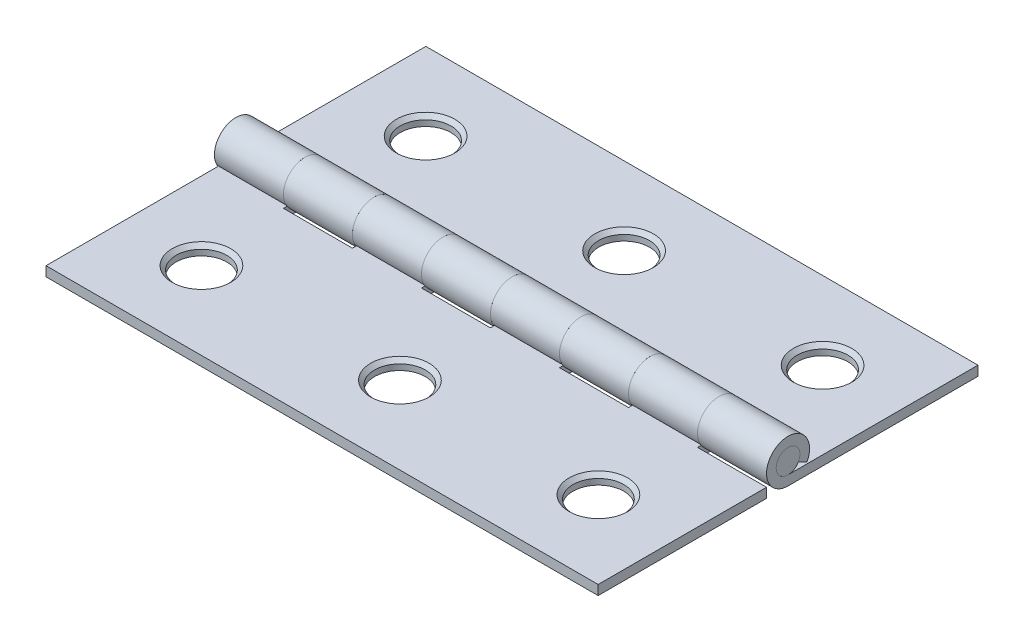
SolidWorks part; units mm, degrees
ref_plane "Front Plane" through (0, 0, 0) normal (0, 0, 1) x (1, 0, 0)
ref_plane "Top Plane" through (0, 0, 0) normal (0, 1, 0) x (1, 0, 0)
ref_plane "Right Plane" through (0, 0, 0) normal (1, 0, 0) x (0, 0, -1)
sketch "Sketch1" plane through (0, 0, 0) normal (0, 1, 0) x (1, 0, 0)
  line L0 (-25.4, 0) -> (25.4, 0) construction
  line L1 (-25.4, -17.4752) -> (-25.4, 17.4752) construction
  line L2 (-25.4, -17.4752) -> (-18.2626, -17.4752) construction
  line L3 (-18.2626, -17.4752) -> (0, -17.4752) construction
  line L4 (0, -17.4752) -> (18.2626, -17.4752) construction
  line L5 (25.4, -17.4752) -> (25.4, -10.3124) construction
  line L6 (18.2626, -17.4752) -> (25.4, -17.4752) construction
  line L7 (-25.4, 17.4752) -> (-18.2626, 17.4752) construction
  line L8 (-18.2626, 17.4752) -> (0, 17.4752) construction
  line L9 (0, 17.4752) -> (18.2626, 17.4752) construction
  line L10 (18.2626, 17.4752) -> (25.4, 17.4752) construction
  line L11 (18.2626, -13.0048) -> (18.2626, -7.62) construction
  line L12 (18.2626, -10.3124) -> (25.4, -10.3124) construction
  point P3 (18.2626, -12.6492)
  point P4 (0, 0)
  point P8 (-25.4, 0)
  point P17 (-19.05, 0)
  point P21 (18.2626, -10.3124)
  dimension "Frame Leaf Height" = 50.8
  dimension "Overall Width" = 34.9504
  dimension "Hole to End 1" = 7.1374
  dimension "Hole Spacing" = 18.2626
  dimension "D3" = 18.2626
  dimension "Hole to End 2" = 7.1374
  dimension "D1" = 7.1374
  dimension "D2" = 7.1374
  dimension "D4" = 18.2626
  dimension "D6" = 18.2626
  dimension "Knuckle Length" = 6.35
  dimension "Hole Chamfer Dia" = 5.3848
  dimension "Hole Center to Pin" = 10.3124
  dimension "Door Leaf Height" = 50.8
  dimension "Frame Leaf Width" = 17.4752
  dimension "Door Leaf Width" = 17.4752
  dimension "Mounting Hole Diameter" = 4.6736
sketch "Sketch2" plane through (0, 0, 0) normal (1, 0, 0) x (0, 0, -1)
  line L2 (0, -1.9812) -> (0, -1.0922) construction
  line L4 (0, 1.0922) -> (0, -1.0922) construction
  point P8 (0, 0)
  dimension "Leaf Thickness" = 0.889
  dimension "Pin Diameter" = 2.1844
sketch "Sketch3" plane through (0, 0, 0) normal (1, 0, 0) x (0, 0, -1)
  line L3 (0, 0) -> (-1.9812, -1.0922) construction
  line L4 (0, -1.9812) -> (-17.4752, -1.9812)
  line L5 (-17.4752, -1.9812) -> (-17.4752, -1.0922)
  line L7 (-17.4752, -1.0922) -> (0, -1.0922)
  line L8 (-17.4752, 0) -> (17.4752, 0) construction
  line L9 (-0.9565, -0.5273) -> (-1.735, -0.9565)
  line L11 (-1.9812, 0) -> (-1.9812, -1.0922) construction
  circle A4 centre (0, 0) radius 1.0922 construction
  circle A5 centre (0, 0) radius 1.9812 construction
  arc A8 (-0.9565, -0.5273) -> (0, -1.0922) centre (0, 0) cw
  arc A9 (-1.735, -0.9565) -> (0, -1.9812) centre (0, 0) cw
  point P0 (-1.735, -0.9565)
  point P13 (-0.9565, -0.5273)
extrude "Boss-Extrude1" add sketch "Sketch3" along normal mid plane 50.8
sketch "Sketch4" plane through (0, 0, 0) normal (0, 1, 0) x (1, 0, 0)
  line L0 (-25.4, -1.9812) -> (25.4, -1.9812) construction
  line L1 (-25.4, -1.9812) -> (25.4, -1.9812) construction
  line L2 (25.4, 1.9812) -> (-25.4, 1.9812) construction
  line L3 (25.4, 1.9812) -> (-25.4, 1.9812) construction
  line L4 (-19.05, -1.9812) -> (-19.05, 1.9812)
  line L6 (-19.05, 1.9812) -> (-12.7, 1.9812)
  line L7 (-12.7, -1.9812) -> (-19.05, -1.9812)
  line L8 (-12.7, 1.9812) -> (-12.7, -1.9812)
  point P8 (-19.05, 0)
  dimension "D1" = 6.35
extrude "Cut-Extrude1" cut sketch "Sketch4" against normal through all both and the other way through all
pattern_linear "LPattern1" count 6 spacing 12.7 along (1, 0, 0) of "Cut-Extrude1"
sketch "Sketch5" plane through (0, -1.0922, 0) normal (0, 1, 0) x (1, 0, 0)
  line L0 (18.2626, -10.3124) -> (-18.2626, -10.3124) construction
  line L1 (0, -10.3124) -> (0, -17.4752) construction
  line L2 (-18.2626, -10.3124) -> (-18.2626, -17.4752) construction
  circle A0 centre (18.2626, -10.3124) radius 2.6924
  circle A1 centre (0, -10.3124) radius 2.6924
  circle A2 centre (-18.2626, -10.3124) radius 2.6924
extrude "Cut-Extrude2" cut sketch "Sketch5" against normal through all draft 45
sketch "Sketch9" plane through (0, 0, 0) normal (0, 1, 0) x (1, 0, 0)
  circle A0 centre (18.2626, -10.3124) radius 2.3368
  circle A1 centre (0, -10.3124) radius 2.3368
  circle A2 centre (-18.2626, -10.3124) radius 2.3368
  dimension "D1" = 4.6736
extrude "Cut-Extrude3" cut sketch "Sketch9" against normal through all both and the other way through all
pattern_circular "CirPattern1" count 2 over 360 about axis through (0, 0, 0) along (0, 1, 0) of bodies 110 107
sketch "Sketch6" plane through (0, 0, 0) normal (1, 0, 0) x (0, 0, -1)
  circle A0 centre (0, 0) radius 1.0922
  dimension "D1" = 2.1844
extrude "Boss-Extrude2" add sketch "Sketch6" along normal mid plane 50.8 separate body
sketch "Sketch7" plane through (0, 0, 0) normal (1, 0, 0) x (0, 0, -1)
  line L0 (-1.0922, 0) -> (1.0922, 0) construction
  line L1 (-17.4752, 0) -> (17.4752, 0) construction
  line L2 (17.4752, -1.0922) -> (17.4752, -1.9812) construction
  line L3 (17.4752, -1.0922) -> (17.4752, -1.9812) construction
  line L4 (17.4752, -1.9812) -> (-17.4752, -1.9812) construction
  line L5 (-17.4752, -1.9812) -> (-17.4752, -1.0922)
  point P6 (0, 0)
  point P8 (1.0922, 0)
  point P9 (-1.0922, 0)
  point P12 (17.4752, -1.0922)
  point P13 (17.4752, -1.9812)
  point P14 (-17.4752, -1.9812)
  dimension "D1" = 2.1844
  dimension "D2" = 34.9504
  dimension "D3" = 0.889
sketch "Sketch8" plane through (0, 0, 0) normal (0, 1, 0) x (1, 0, 0)
  line L0 (-20.955, -10.3124) -> (-15.5702, -10.3124) construction
  line L1 (-2.6924, -10.3124) -> (2.6924, -10.3124) construction
  line L2 (15.5702, -10.3124) -> (20.955, -10.3124) construction
  line L3 (-18.2626, -7.62) -> (-18.2626, -13.0048) construction
  line L4 (0, -7.62) -> (0, -13.0048) construction
  line L5 (18.2626, -7.62) -> (18.2626, -13.0048) construction
  line L6 (-18.2626, 13.0048) -> (-18.2626, 7.62) construction
  line L7 (-20.955, 10.3124) -> (-15.5702, 10.3124) construction
  line L8 (0, 13.0048) -> (0, 7.62) construction
  line L9 (-2.6924, 10.3124) -> (2.6924, 10.3124) construction
  line L10 (18.2626, 13.0048) -> (18.2626, 7.62) construction
  line L11 (15.5702, 10.3124) -> (20.955, 10.3124) construction
  line L12 (18.2626, 10.3124) -> (20.1664, 12.2162) construction
  circle A1 centre (-18.2626, -10.3124) radius 2.6924 construction
  circle A2 centre (0, -10.3124) radius 2.6924 construction
  circle A3 centre (18.2626, -10.3124) radius 2.6924 construction
  circle A4 centre (-18.2626, 10.3124) radius 2.6924 construction
  circle A5 centre (0, 10.3124) radius 2.6924 construction
  circle A6 centre (18.2626, 10.3124) radius 2.6924 construction
  circle A7 centre (18.2626, 10.3124) radius 2.6924 construction
  point P2 (-25.4, 0)
  point P7 (-18.2626, -10.3124)
  point P13 (0, -10.3124)
  point P19 (18.2626, -10.3124)
  point P25 (-25.4, 17.4752)
  point P26 (25.4, 17.4752)
  point P28 (-25.4, -17.4752)
  point P30 (25.4, -17.4752)
  point P32 (-20.955, -10.3124)
  point P33 (-18.2626, -7.62)
  point P34 (-15.5702, -10.3124)
  point P35 (-18.2626, -13.0048)
  point P36 (0, -13.0048)
  point P37 (-2.6924, -10.3124)
  point P38 (0, -7.62)
  point P39 (2.6924, -10.3124)
  point P40 (20.955, -10.3124)
  point P41 (18.2626, -13.0048)
  point P42 (15.5702, -10.3124)
  point P43 (18.2626, -7.62)
  point P66 (0, -17.4752)
  point P67 (18.2626, -17.4752)
  point P69 (-18.2626, -17.4752)
  point P71 (-18.2626, 17.4752)
  point P73 (-18.2626, 10.3124)
  point P75 (0, 10.3124)
  point P76 (18.2626, 10.3124)
  point P77 (18.2626, 17.4752)
  point P78 (0, 17.4752)
  point P82 (-18.2626, 13.0048)
  point P83 (-20.955, 10.3124)
  point P84 (-18.2626, 7.62)
  point P85 (-15.5702, 10.3124)
  point P86 (0, 7.62)
  point P87 (-2.6924, 10.3124)
  point P88 (0, 13.0048)
  point P89 (2.6924, 10.3124)
  point P90 (18.2626, 7.62)
  point P91 (15.5702, 10.3124)
  point P92 (18.2626, 13.0048)
  point P93 (20.955, 10.3124)
  point P97 (20.1664, 12.2162)
  dimension "D1" = 45
equation "\"D3@Sketch1\"=\"Hole Spacing@Sketch1\""
equation "\"D1@Sketch1\"=\"Hole to End 1@Sketch1\""
equation "\"D2@Sketch1\"=\"Hole to End 2@Sketch1\""
equation "\"D4@Sketch1\"=\"Hole Spacing@Sketch1\""
equation "\"D6@Sketch1\"=\"D4@Sketch1\""
equation "\"D1@Boss-Extrude1\" = \"Frame Leaf Height@Sketch1\""
equation "\"D1@Sketch4\"=\"Knuckle Length@Sketch1\""
equation "\"D3@LPattern1\"=\"Knuckle Length@Sketch1\"*2"
equation "\"D1@Sketch6\"=\"Pin Diameter@Sketch2\""
equation "\"D1@Boss-Extrude2\" = \"Frame Leaf Height@Sketch1\""
equation "\"D1@Sketch7\"=\"Pin Diameter@Sketch2\""
equation "\"D2@Sketch7\"=\"Overall Width@Sketch1\""
equation "\"D3@Sketch7\"=\"Leaf Thickness@Sketch2\""
equation "\"Knuckle Length@Sketch1\" = \"Frame Leaf Height@Sketch1\" / 8"
equation "\"Hole to End 2@Sketch1\"=\"Hole to End 1@Sketch1\""
equation "\"D1@Sketch9\"=\"Mounting Hole Diameter@Sketch1\""
